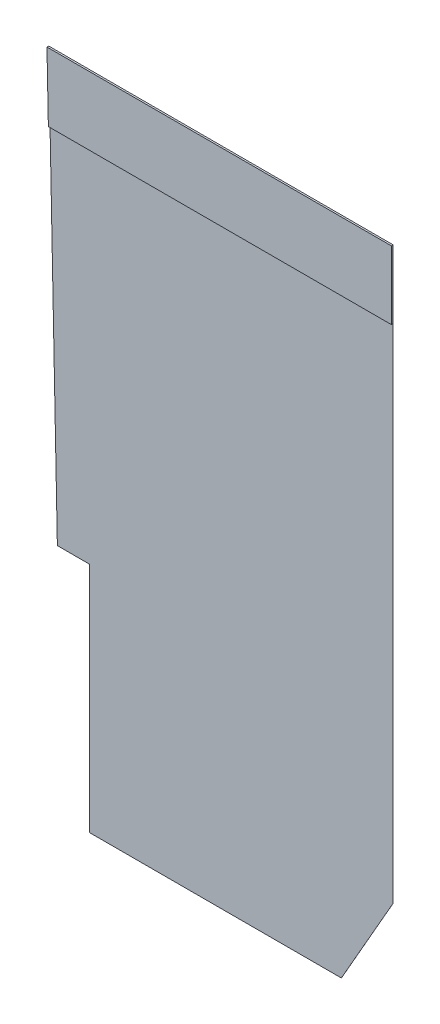
SolidWorks part; units mm, degrees
ref_plane "Alzado" through (0, 0, 0) normal (0, 0, 1) x (1, 0, 0)
ref_plane "Planta" through (0, 0, 0) normal (0, 1, 0) x (1, 0, 0)
ref_plane "Vista lateral" through (0, 0, 0) normal (1, 0, 0) x (0, 0, -1)
sketch "Croquis1" plane through (0, 0, 0) normal (0, 0, 1) x (1, 0, 0)
  line L0 (0, 0) -> (0, 3549.65)
  line L1 (0, 3549.65) -> (-488.95, 3549.65)
  line L2 (-488.95, 3549.65) -> (-622.3, 10090.15)
  line L3 (-622.3, 10090.15) -> (4635.5, 10090.15)
  line L4 (4635.5, 10090.15) -> (4635.5, 1377.95)
  line L5 (4635.5, 1377.95) -> (3848.1, 0)
  line L6 (3848.1, 0) -> (0, 0)
  point P10 (2507.4841, -86.7925)
  dimension "D1" = 5257.8
  dimension "D2" = 8712.2
  dimension "D3" = 787.4
  dimension "D4" = 1377.95
  dimension "D5" = 4635.5
  dimension "D6" = 488.95
  dimension "D7" = 3549.65
  dimension "D8" = 6540.5
  dimension "D9" = 88.832
  dimension "D10" = 119.745
  dimension "D11" = 150.255
  dimension "D12" = 91.168
extrude "Saliente-Extruir1" add sketch "Croquis1" along normal blind 1.5875
sketch "Croquis2" plane through (0, 0, 1.5875) normal (0, 0, 1) x (1, 0, 0)
  line L0 (4635.5, 9048.75) -> (-601.0676, 9048.75)
  line L1 (4635.5, 1377.95) -> (4635.5, 10090.15) construction
  line L2 (-622.3, 10090.15) -> (-488.95, 3549.65) construction
  line L3 (4635.5, 10090.15) -> (-622.3, 10090.15) construction
  line L4 (-601.0676, 9048.75) -> (-622.3, 10090.15)
  line L5 (-622.3, 10090.15) -> (4635.5, 10090.15)
  line L6 (4635.5, 10090.15) -> (4635.5, 9048.75)
  dimension "D1" = 1041.4
extrude "Saliente-Extruir2" add sketch "Croquis2" along normal blind 25.4
